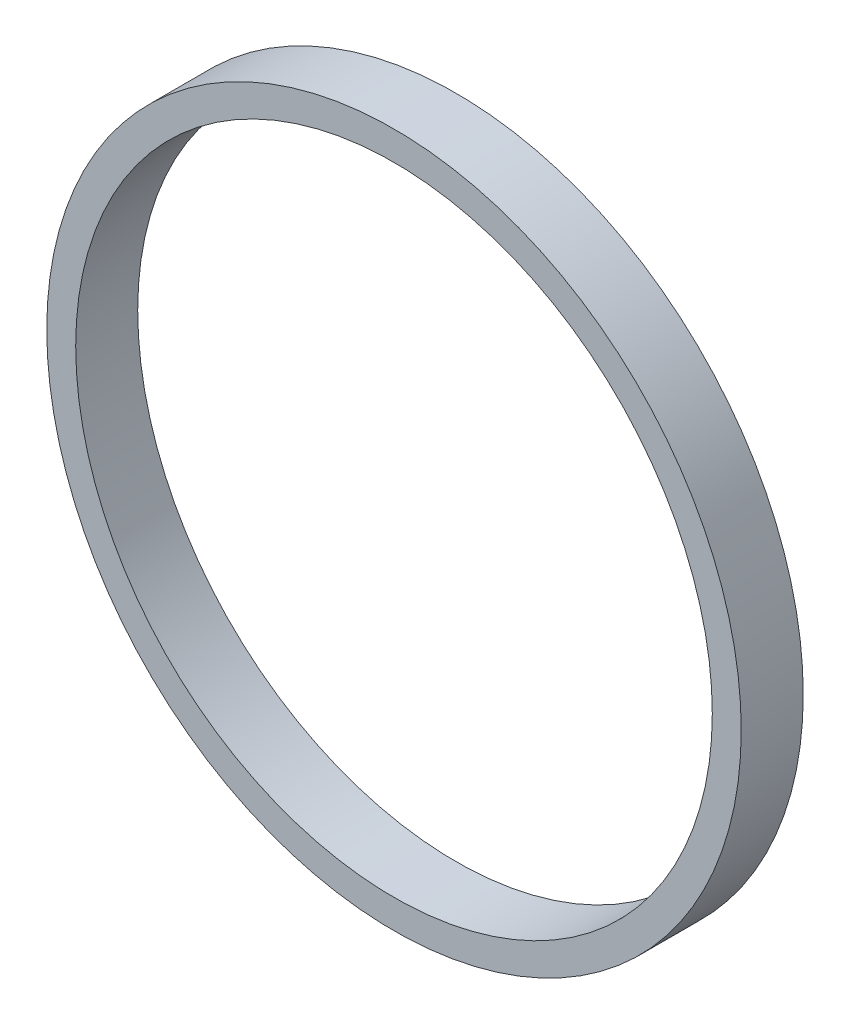
SolidWorks part; units mm, degrees
ref_plane "Front Plane" through (0, 0, 0) normal (0, 0, 1) x (1, 0, 0)
ref_plane "Top Plane" through (0, 0, 0) normal (0, 1, 0) x (1, 0, 0)
ref_plane "Right Plane" through (0, 0, 0) normal (1, 0, 0) x (0, 0, -1)
sketch "Sketch1" plane through (0, 0, 0) normal (0, 0, 1) x (1, 0, 0)
  circle A0 centre (0, 0) radius 84
  circle A1 centre (0, 0) radius 77
  dimension "D1" = 168
  dimension "D2" = 154
extrude "Boss-Extrude1" add sketch "Sketch1" along normal blind 15
